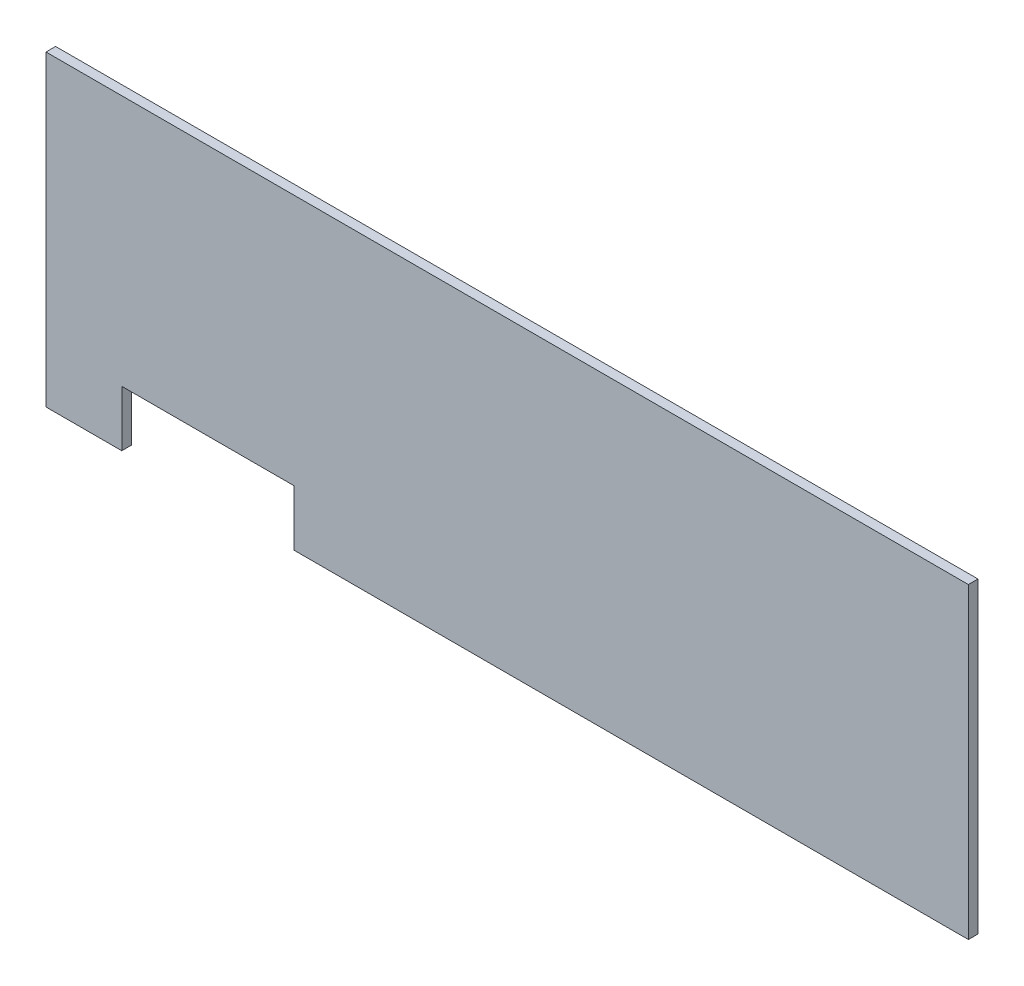
SolidWorks part; units mm, degrees
ref_plane "Front Plane" through (0, 0, 0) normal (0, 0, 1) x (1, 0, 0)
ref_plane "Top Plane" through (0, 0, 0) normal (0, 1, 0) x (1, 0, 0)
ref_plane "Right Plane" through (0, 0, 0) normal (1, 0, 0) x (0, 0, -1)
sketch "Sketch1" plane through (0, 0, 0) normal (0, 0, 1) x (1, 0, 0)
  line L0 (-70.4905, -50.8) -> (152.4, -50.8)
  line L1 (-152.4, -50.8) -> (-127.3628, -50.8)
  line L2 (-152.4, -50.8) -> (-152.4, 50.8)
  line L3 (-152.4, 50.8) -> (152.4, 50.8)
  line L4 (152.4, -50.8) -> (152.4, 50.8)
  line L5 (-152.4, -50.8) -> (152.4, 50.8) construction
  line L6 (-152.4, 50.8) -> (152.4, -50.8) construction
  line L8 (-127.3628, -50.8) -> (-127.3628, -32.3486)
  line L9 (-127.3628, -32.3486) -> (-70.4905, -32.3486)
  line L10 (-70.4905, -50.8) -> (-70.4905, -32.3486)
  point P0 (0, 0)
  dimension "D1" = 304.8
  dimension "D2" = 101.6
extrude "Boss-Extrude1" add sketch "Sketch1" along normal blind 3.175
